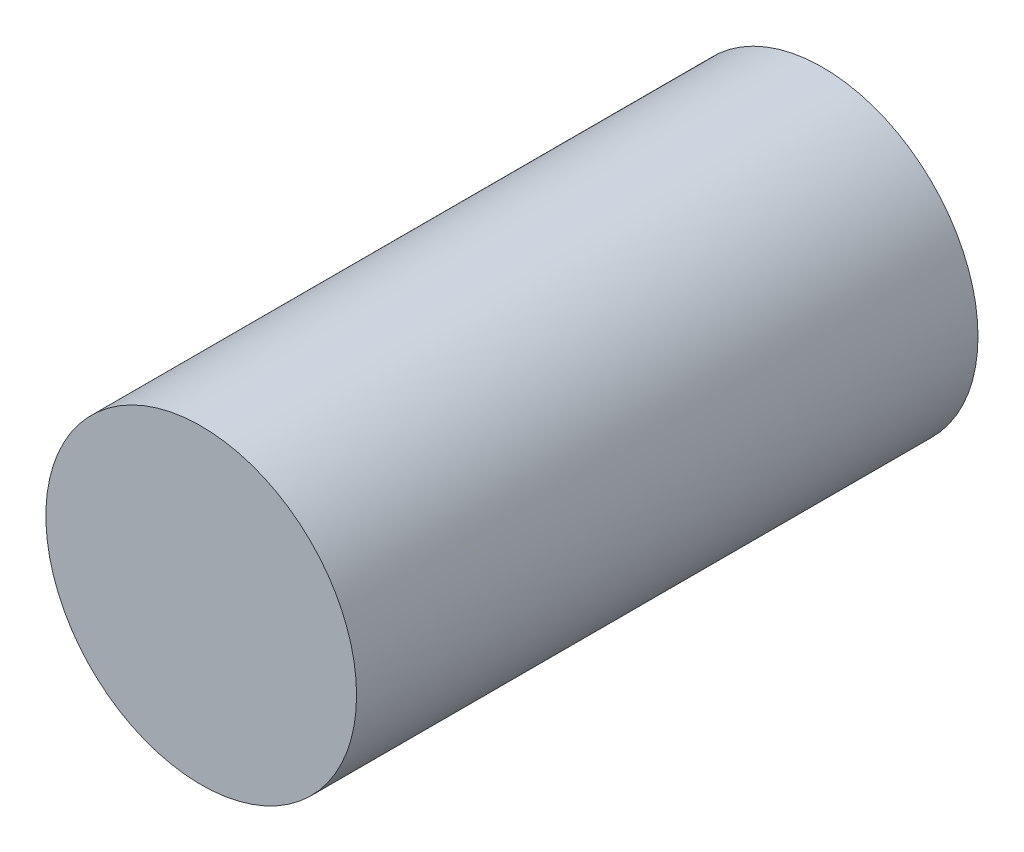
SolidWorks part; units mm, degrees
ref_plane "Alzado" through (0, 0, 0) normal (0, 0, 1) x (1, 0, 0)
ref_plane "Planta" through (0, 0, 0) normal (0, 1, 0) x (1, 0, 0)
ref_plane "Vista lateral" through (0, 0, 0) normal (1, 0, 0) x (0, 0, -1)
sketch "Croquis1" plane through (0, 0, 0) normal (0, 0, 1) x (1, 0, 0)
  circle A0 centre (0, 0) radius 0.5
  dimension "D1" = 1
extrude "Saliente-Extruir1" add sketch "Croquis1" along normal blind 2
